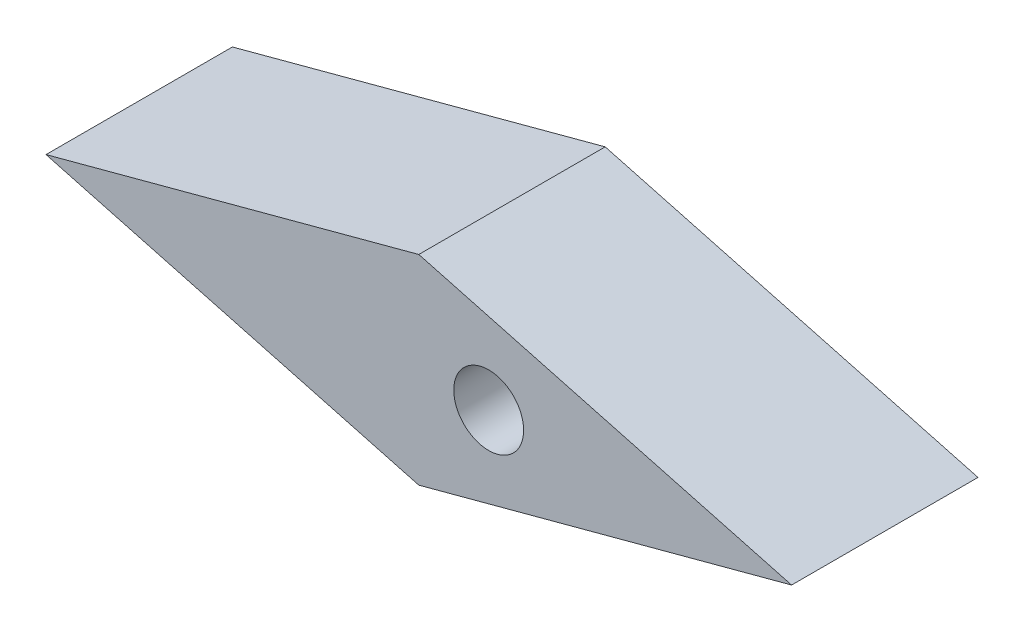
SolidWorks part; units mm, degrees
ref_plane "前视基准面" through (0, 0, 0) normal (0, 0, 1) x (1, 0, 0)
ref_plane "上视基准面" through (0, 0, 0) normal (0, 1, 0) x (1, 0, 0)
ref_plane "右视基准面" through (0, 0, 0) normal (1, 0, 0) x (0, 0, -1)
sketch "草图1" plane through (0, 0, 0) normal (0, 0, 1) x (1, 0, 0)
  line L0 (-16, 0) -> (0, 4.2872)
  line L1 (0, 4.2872) -> (16, 0)
  line L2 (16, 0) -> (0, -4.2872)
  line L3 (0, -4.2872) -> (-16, 0)
  line L4 (-24.599, 0) -> (28.529, 0) construction
  dimension "D1" = 30
  dimension "D2" = 15
  dimension "D3" = 30
  dimension "D4" = 16
extrude "凸台-拉伸1" add sketch "草图1" along normal blind 8
sketch "草图2" plane through (0, 0, 0) normal (0, 0, -1) x (-1, 0, 0)
  circle A0 centre (-3, 0) radius 1.5
  dimension "D1" = 3
  dimension "D2" = 13
extrude "切除-拉伸1" cut sketch "草图2" against normal through all
cosmetic thread "装饰螺纹线1" parameters "D1"=5, "D2"=9
sketch "草图3" plane through (0, 0, 0) normal (0, 0, -1) x (-1, 0, 0)
  circle A0 centre (-3, 0) radius 2.5
  dimension "D1" = 5
extrude "切除-拉伸2" cut sketch "草图3" against normal blind 3
sketch "草图4" plane through (0, 0, 0) normal (0, 0, -1) x (-1, 0, 0)
  line L0 (-15.8928, 0) -> (17.0838, 0) construction
  line L1 (0, 8.3942) -> (0, -6.6734) construction
